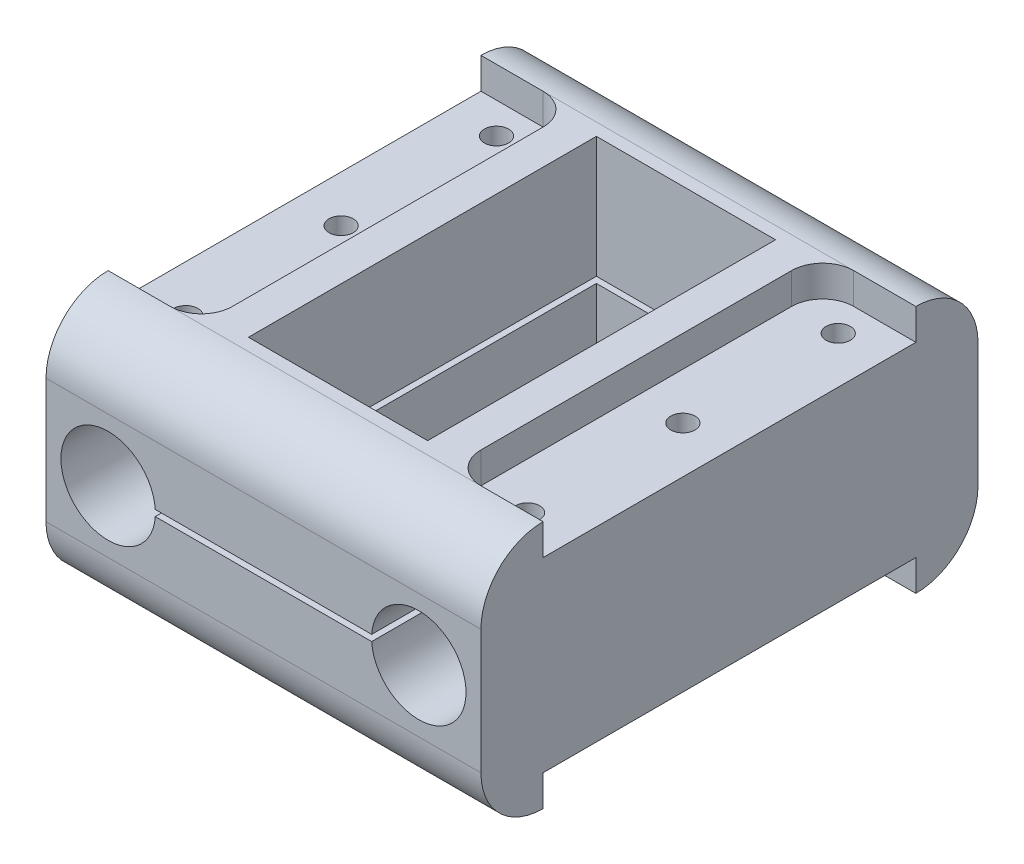
SolidWorks part; units mm, degrees
ref_plane "Front Plane" through (0, 0, 0) normal (0, 0, 1) x (1, 0, 0)
ref_plane "Top Plane" through (0, 0, 0) normal (0, 1, 0) x (1, 0, 0)
ref_plane "Right Plane" through (0, 0, 0) normal (1, 0, 0) x (0, 0, -1)
sketch "Sketch1" plane through (0, 0, 0) normal (0, 0, 1) x (1, 0, 0)
  line L0 (0, 0) -> (50, 0) construction
  line L2 (-10, 20) -> (60, 20)
  line L3 (-10, 20) -> (-10, -20)
  line L4 (-10, -20) -> (60, -20)
  line L5 (60, 20) -> (60, -20)
  line L6 (-10, 20) -> (60, -20) construction
  line L7 (-10, -20) -> (60, 20) construction
  circle A0 centre (0, 0) radius 7.6
  circle A1 centre (50, 0) radius 7.6
  point P5 (25, 0)
  dimension "D1" = 15.2
  dimension "D2" = 50
  dimension "D3" = 70
  dimension "D4" = 40
extrude "Boss-Extrude1" add sketch "Sketch1" along normal blind 80
fillet "Fillet1" radius 10 4 edges at (25, 20, 80) (25, -20, 80) (25, -20, 0) (25, 20, 0)
sketch "Sketch12" plane through (0, 0, 80) normal (0, 0, 1) x (1, 0, 0)
  line L0 (7.6, 0) -> (42.4, 0)
  line L1 (7.6, 0) -> (3.1193, 0)
  line L2 (42.4, 0) -> (46.982, 0)
  circle A0 centre (0, 0) radius 7.6 construction
  circle A1 centre (50, 0) radius 7.6 construction
extrude "Cut-Extrude-Thin1" cut sketch "Sketch12" against normal blind 95 and the other way through all thin thin type mid plane wall 1
sketch "Sketch21" plane through (-10, 0, 0) normal (-1, 0, 0) x (0, 0, 1)
  circle A0 centre (10, -14) radius 1.95
  circle A1 centre (70, -14) radius 1.95
  dimension "D1" = 3.9
  dimension "D2" = 3.9
  dimension "D3" = 6
  dimension "D4" = 6
sketch "Sketch24" plane through (0, 0.5, 0) normal (0, -1, 0) x (1, 0, 0)
  line L1 (10.5835, 68) -> (10.5835, 12)
  line L3 (39.4165, 12) -> (39.4165, 68)
  line L4 (7.5835, 80) -> (7.5835, 0)
  line L5 (7.5835, 0) -> (42.4165, 0)
  line L6 (42.4165, 0) -> (42.4165, 80)
  line L7 (42.4165, 80) -> (7.5835, 80)
  line L8 (7.5835, 80) -> (7.5835, 0)
  line L9 (7.5835, 0) -> (42.4165, 0)
  line L10 (42.4165, 0) -> (42.4165, 80)
  line L11 (42.4165, 80) -> (7.5835, 80)
  line L12 (10.5835, 68) -> (39.4165, 68)
  line L13 (10.5835, 12) -> (39.4165, 12)
  line L14 (10.5835, 77) -> (10.5835, 3) construction
  line L15 (39.4165, 3) -> (39.4165, 77) construction
  line L16 (39.4165, 77) -> (10.5835, 77) construction
  line L17 (10.5835, 3) -> (39.4165, 3) construction
  dimension "D3" = 12
  dimension "D4" = 12
  dimension "D1" = 0
  dimension "D2" = 3
extrude "Cut-Extrude15" cut sketch "Sketch24" against normal blind 40 and the other way blind 39
sketch "Sketch27" plane through (0, 20, 0) normal (0, 1, 0) x (1, 0, 0)
  line L0 (-10, -70) -> (60, -70) construction
  line L1 (-10, -10) -> (0, -10)
  line L2 (-10, -10) -> (-10, -70)
  line L3 (-10, -70) -> (0, -70)
  line L4 (5, -15) -> (5, -65)
  arc A0 (0, -70) -> (5, -65) centre (0, -65) ccw
  arc A1 (0, -10) -> (5, -15) centre (0, -15) cw
  point P9 (5, -70)
  point P12 (5, -10)
  dimension "D2" = 5
  dimension "D1" = 15
extrude "Cut-Extrude17" cut sketch "Sketch27" against normal blind 5
sketch "Sketch28" plane through (0, 15, 0) normal (0, 1, 0) x (1, 0, 0)
  line L0 (5, -15) -> (-2.5, -15) construction
  line L1 (5, -40) -> (-2.5, -40) construction
  line L2 (5, -65) -> (5, -15) construction
  line L3 (5, -65) -> (-2.5, -65) construction
  circle A0 centre (-2.5, -15) radius 1.95
  circle A1 centre (-2.5, -40) radius 1.95
  circle A2 centre (-2.5, -65) radius 1.95
  dimension "D2" = 3.9
  dimension "D1" = 7.5
extrude "Cut-Extrude18" cut sketch "Sketch28" against normal blind 20
ref_plane "Plane2" through (25, 0, 0) normal (-1, 0, 0) x (0, 0, 1)
mirror "Mirror1" about plane through (25, 0, 0) normal (-1, 0, 0) of "Cut-Extrude17", "Cut-Extrude18"
mirror "Mirror2" about plane through (0, 0, 0) normal (0, 1, 0) of "Mirror1", "Cut-Extrude17", "Cut-Extrude18"
